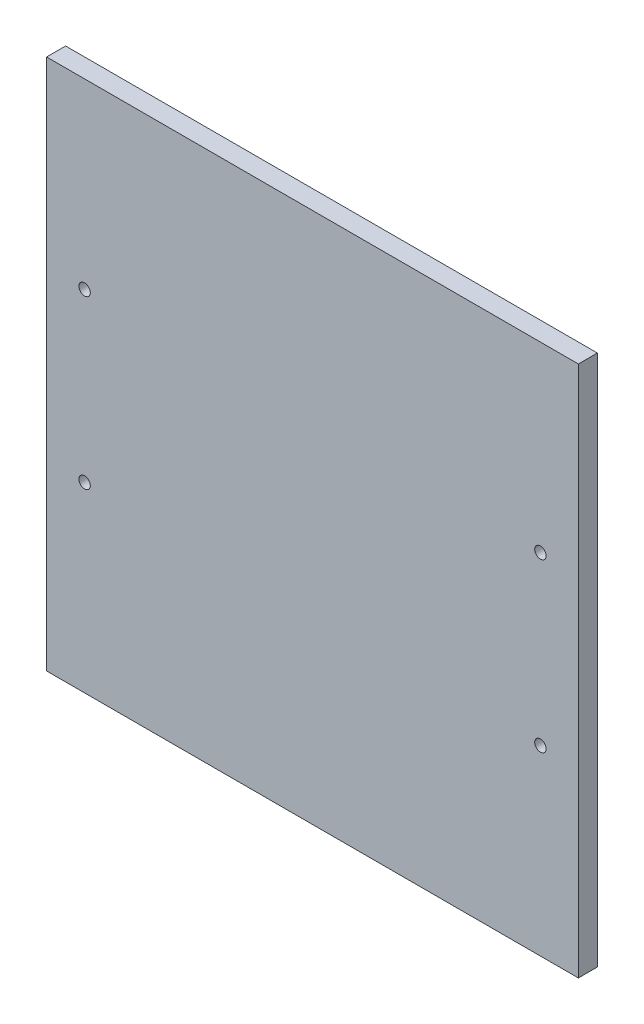
SolidWorks part; units mm, degrees
material "Ceramic Porcelain"
ref_plane "Front Plane" through (0, 0, 0) normal (0, 0, 1) x (1, 0, 0)
ref_plane "Top Plane" through (0, 0, 0) normal (0, 1, 0) x (1, 0, 0)
ref_plane "Right Plane" through (0, 0, 0) normal (1, 0, 0) x (0, 0, -1)
sketch "Sketch1" plane through (0, 0, 0) normal (0, 0, 1) x (1, 0, 0)
  line L0 (140, 70) -> (0, 70) construction
  line L1 (0, 0) -> (140, 0)
  line L2 (0, 0) -> (0, 140)
  line L3 (0, 140) -> (140, 140)
  line L4 (140, 0) -> (140, 140)
  dimension "D1" = 140
  dimension "D5" = 140
extrude "Boss-Extrude1" add sketch "Sketch1" along normal blind 5
hole_wizard "CSK for M3 Flat Head Machine Screw1" positions "Sketch6" profile "Sketch5" countersink size "M3" standard "Ansi Metric" end condition through all
sketch "Sketch6" plane through (0, 0, 0) normal (0, 0, -1) x (-1, 0, 0)
  line L0 (6.0733, 70) -> (-132.5, 70) construction
  line L5 (-130, 92) -> (-130, 48) construction
  line L9 (-70, 140) -> (-70, 0) construction
  line L10 (-140, 140) -> (0, 140) construction
  line L11 (0, 0) -> (-140, 0) construction
  line L13 (-10, 92) -> (-10, 48) construction
  line L14 (-146.0733, 70) -> (-7.5, 70) construction
  point P20 (-130, 92)
  point P22 (-130, 48)
  point P48 (-10, 92)
  point P50 (-10, 48)
  dimension "D1" = 60
  dimension "D3" = 22
  dimension "D4" = 44
sketch "Sketch5" plane through (130, 92, 0) normal (1, 0, 0) x (0, 1, 0)
  line L0 (0, 0) -> (0, 5)
  line L1 (0, 5) -> (1.5, 5)
  line L2 (1.5, 5) -> (1.5, 2.5)
  line L3 (1.5, 2.5) -> (4, 0)
  line L5 (4, 0) -> (0, 0)
  line L6 (-1.5, 2.5) -> (-4, 0) construction
  line L11 (0, -6.35) -> (0, 107.95) construction
  dimension "Thru Hole Dia." = 3
  dimension "Thru Hole Depth" = 5
  dimension "Near C'Sink Dia." = 8
  dimension "Near C'Sink Angle" = 90
sketch "Sketch7" plane through (0, 0, 0) normal (0, 0, -1) x (-1, 0, 0)
  line L0 (-70, 140) -> (-70, 0) construction
  line L1 (-140, 140) -> (0, 140) construction
  line L2 (0, 0) -> (-140, 0) construction
  line L3 (-61.8, 132) -> (-78.2, 132) construction
  circle A0 centre (-78.2, 132) radius 1.5
  circle A1 centre (-61.8, 132) radius 1.5
  dimension "D2" = 3
  dimension "D3" = 8.2
  dimension "D1" = 8.2
  dimension "D4" = 8
extrude "Cut-Extrude1" [suppressed] cut sketch "Sketch7" against normal through all
